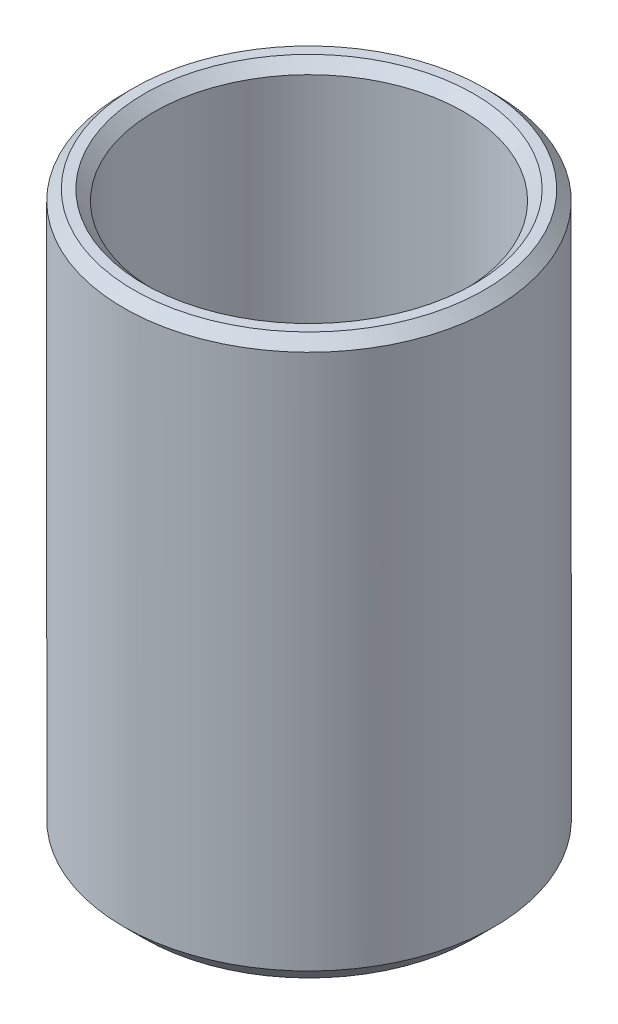
SolidWorks part; units mm, degrees
material "ПВХ Жесткий"
ref_plane "Спереди" through (0, 0, 0) normal (0, 0, 1) x (1, 0, 0)
ref_plane "Сверху" through (0, 0, 0) normal (0, 1, 0) x (1, 0, 0)
ref_plane "Справа" through (0, 0, 0) normal (1, 0, 0) x (0, 0, -1)
sketch "Эскиз1" plane through (0, 0, 0) normal (0, 0, 1) x (1, 0, 0)
  line L0 (0, 0) -> (-18, 0)
  line L1 (-18, 0) -> (-18, 55)
  line L2 (-18, 55) -> (-15, 55)
  line L3 (-15, 55) -> (-15, 3)
  line L4 (-15, 3) -> (0, 3)
  line L5 (0, 3) -> (0, 0)
  line L6 (0, 3) -> (0, 55) construction
  line L7 (-15, 55) -> (0, 55) construction
  dimension "D1" = 15
  dimension "D2" = 3
  dimension "D3" = 3
  dimension "D4" = 52
revolve "Повернуть1" add sketch "Эскиз1" angle 360 about L6
sketch "Эскиз2" plane through (0, 55, 0) normal (0, 1, 0) x (1, 0, 0)
  line L0 (18, 0) -> (-18, 0) construction
  circle A0 centre (0, 0) radius 18 construction
ref_plane "Симм Кювета" through (0, 0, 0) normal (0, 0, -1) x (-1, 0, 0)
chamfer "Фаска1" distance 2 angle 45 1 edges at (0, 0, -18)
chamfer "Фаска2" distance 1 angle 45 2 edges at (0, 55, -18) (0, 55, -15)
chamfer "Фаска3" distance 1 angle 45 1 edges at (0, 3, -15)
